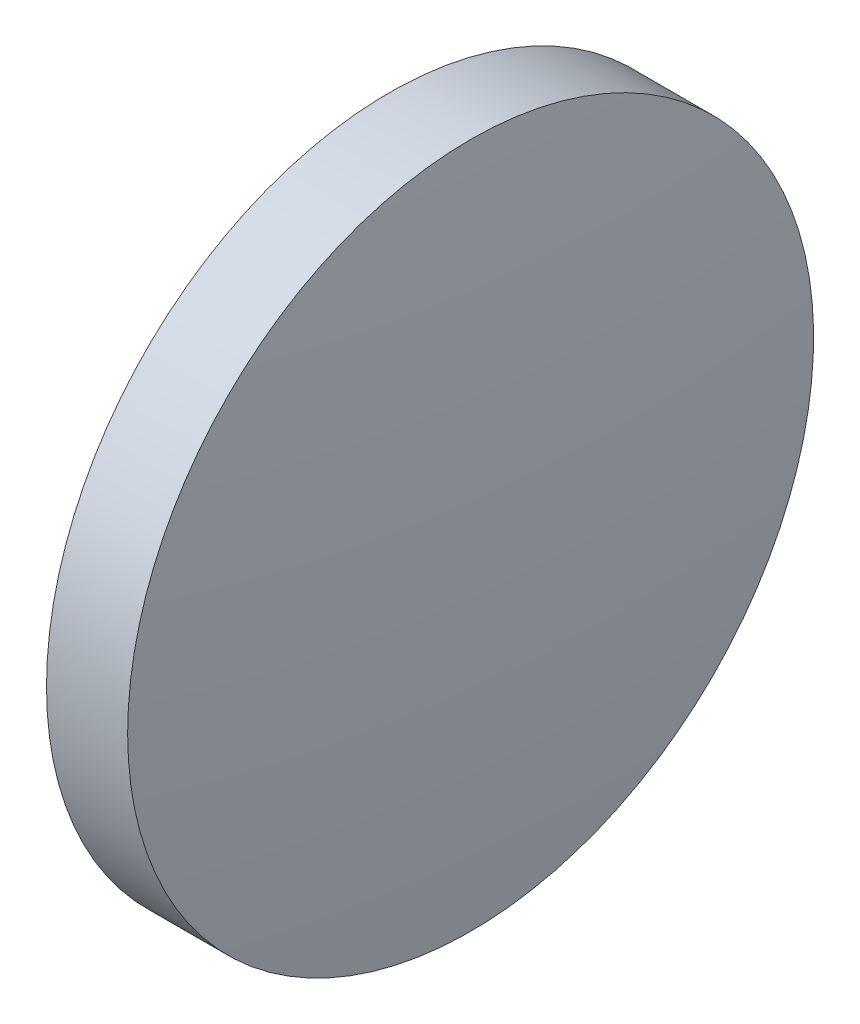
SolidWorks part; units mm, degrees
ref_plane "前视基准面" through (0, 0, 0) normal (0, 0, 1) x (1, 0, 0)
ref_plane "上视基准面" through (0, 0, 0) normal (0, 1, 0) x (1, 0, 0)
ref_plane "右视基准面" through (0, 0, 0) normal (1, 0, 0) x (0, 0, -1)
sketch "草图1" plane through (0, 0, 0) normal (0, 0, 1) x (1, 0, 0)
  line L0 (110.1654, 65.2336) -> (128.9614, 65.2336) construction
  line L1 (115.7736, 65.2336) -> (115.7736, 77.9336)
  line L2 (115.7736, 77.9336) -> (118.7777, 77.9336)
  line L3 (119.4836, 65.2336) -> (115.7736, 65.2336)
  arc A0 (119.4836, 65.2336) -> (118.7777, 77.9336) centre (4.8806, 65.2336) ccw
  dimension "D1" = 114.603
revolve "旋转1" add sketch "草图1" angle 360 about L0
